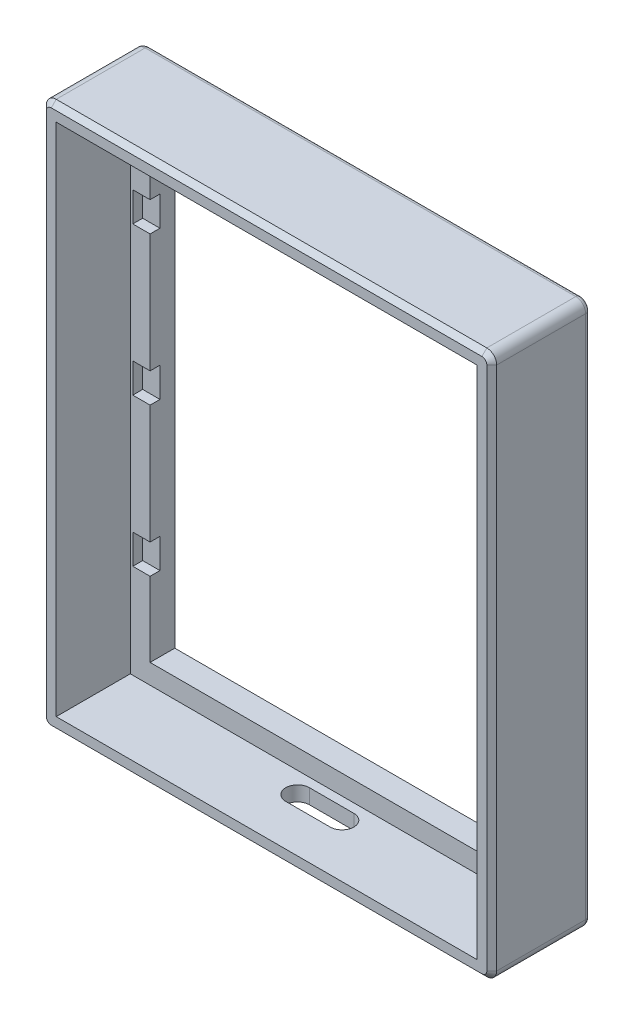
SolidWorks part; units mm, degrees
ref_plane "前视基准面" through (0, 0, 0) normal (0, 0, 1) x (1, 0, 0)
ref_plane "上视基准面" through (0, 0, 0) normal (0, 1, 0) x (1, 0, 0)
ref_plane "右视基准面" through (0, 0, 0) normal (1, 0, 0) x (0, 0, -1)
other "Configuration Table"
sketch "Model" plane through (0, 0, 0) normal (0, 0, 1) x (1, 0, 0)
  line L0 (-4.3804, 99.9831) -> (80.769, 99.9831)
  line L1 (80.769, -4.2164) -> (80.769, 99.9831)
  line L2 (-4.3804, -4.2164) -> (80.769, -4.2164)
  line L3 (-4.3804, -4.2164) -> (-4.3804, 99.9831)
  line L164 (-0.3804, 95.9831) -> (76.769, 95.9831)
  line L165 (-0.3804, -0.2164) -> (-0.3804, 95.9831)
  line L166 (-0.3804, -0.2164) -> (76.769, -0.2164)
  line L167 (76.769, -0.2164) -> (76.769, 95.9831)
  dimension "D1" = 77.1493
  dimension "D2" = 96.1995
  dimension "D3" = 4
extrude "凸台-拉伸2" add sketch "Model" along normal blind 5
sketch "草图2" plane through (0, 0, 5) normal (0, 0, 1) x (1, 0, 0)
  line L0 (-0.3804, 95.9831) -> (-0.3804, -0.2164) construction
  line L1 (-3.8804, 80.8834) -> (-0.3804, 80.8834)
  line L2 (-3.8804, 80.8834) -> (-3.8804, 74.8834)
  line L3 (-3.8804, 74.8834) -> (-0.3804, 74.8834)
  line L4 (-0.3804, 80.8834) -> (-0.3804, 74.8834)
  line L5 (-3.3804, 80.3834) -> (-0.3804, 80.3834) construction
  line L6 (-3.3804, 75.3834) -> (-3.3804, 80.3834) construction
  line L7 (-0.3804, 75.3834) -> (-3.3804, 75.3834) construction
  line L9 (76.769, 80.8834) -> (76.769, 74.8834)
  line L10 (80.269, 74.8834) -> (76.769, 74.8834)
  line L11 (80.269, 80.8834) -> (80.269, 74.8834)
  line L12 (80.269, 80.8834) -> (76.769, 80.8834)
  line L13 (-3.8804, 50.8834) -> (-0.3803, 50.8834)
  line L14 (-3.8804, 50.8834) -> (-3.8804, 44.8834)
  line L15 (-3.8804, 44.8834) -> (-0.3803, 44.8834)
  line L16 (-0.3803, 50.8834) -> (-0.3803, 44.8834)
  line L17 (76.769, 50.8834) -> (76.769, 44.8834)
  line L18 (80.269, 44.8834) -> (76.769, 44.8834)
  line L19 (80.269, 50.8834) -> (80.269, 44.8834)
  line L20 (80.269, 50.8834) -> (76.769, 50.8834)
  line L21 (-3.8804, 20.8834) -> (-0.3803, 20.8834)
  line L22 (-3.8804, 20.8834) -> (-3.8804, 14.8834)
  line L23 (-3.8804, 14.8834) -> (-0.3803, 14.8834)
  line L24 (-0.3803, 20.8834) -> (-0.3803, 14.8834)
  line L25 (76.769, 20.8834) -> (76.769, 14.8834)
  line L26 (80.269, 14.8834) -> (76.769, 14.8834)
  line L27 (80.269, 20.8834) -> (80.269, 14.8834)
  line L28 (80.269, 20.8834) -> (76.769, 20.8834)
  dimension "D1" = 0.5
  dimension "D2" = 0.5
  dimension "D3" = 0.5
extrude "切除-拉伸1" cut sketch "草图2" against normal blind 2
sketch "草图4" plane through (0, 0, 0) normal (0, 0, -1) x (-1, 0, 0)
  line L0 (-83.769, 102.9831) -> (-83.769, -7.2164)
  line L1 (-80.769, 99.9831) -> (4.3804, 99.9831)
  line L2 (-80.769, 99.9831) -> (-80.769, -4.2164)
  line L3 (-80.769, -4.2164) -> (4.3804, -4.2164)
  line L4 (4.3804, 99.9831) -> (4.3804, -4.2164)
  line L5 (-83.769, -7.2164) -> (7.3804, -7.2164)
  line L6 (7.3804, 102.9831) -> (7.3804, -7.2164)
  line L7 (-83.769, 102.9831) -> (7.3804, 102.9831)
  dimension "D1" = 3
extrude "凸台-拉伸5" add sketch "草图4" against normal blind 20
fillet "圆角1" radius 2 4 edges at (-7.3804, 102.9831, 10) (83.769, 102.9831, 10) (83.769, -7.2164, 10) (-7.3804, -7.2164, 10)
chamfer "倒角1" distance 1 8 edges at (38.1943, -7.2164, 20) (-6.7946, -6.6306, 20) (83.1832, -6.6306, 20) (-7.3804, 47.8834, 20) (83.769, 47.8834, 20) (-6.7946, 102.3973, 20) (83.1832, 102.3973, 20) (38.1943, 102.9831, 20)
fillet "圆角2" radius 1 8 edges at (-6.7946, 102.3973, 0) (-7.3804, 47.8834, 0) (-6.7946, -6.6306, 0) (38.1943, -7.2164, 0) (83.1832, -6.6306, 0) (83.769, 47.8834, 0) (83.1832, 102.3973, 0) (38.1943, 102.9831, 0)
extrude "切除-拉伸2" cut sketch "草图5" against normal blind 10
sketch "草图5" plane through (76.3887, -7.2164, 20) normal (0, -1, 0) x (-1, 0, 0)
  line L0 (-5.3803, 10) -> (81.769, 10) construction
  line L3 (38.1943, 15) -> (38.1943, 27.445) construction
  line L5 (14.7486, 12.652) -> (54.2423, 12.652) construction
  line L8 (38.1943, 12.652) -> (38.1943, 8.888) construction
  line L9 (42.6943, 10.77) -> (33.6943, 10.77)
  line L10 (33.6943, 10.77) -> (42.6943, 10.77) construction
  line L11 (33.6943, 13.17) -> (42.6943, 13.17)
  line L12 (33.6943, 8.37) -> (42.6943, 8.37)
  arc A0 (33.6943, 13.17) -> (33.6943, 8.37) centre (33.6943, 10.77) ccw
  arc A1 (42.6943, 8.37) -> (42.6943, 13.17) centre (42.6943, 10.77) ccw
  point P17 (38.1943, 10.77)
  point P21 (38.1943, 10.77)
